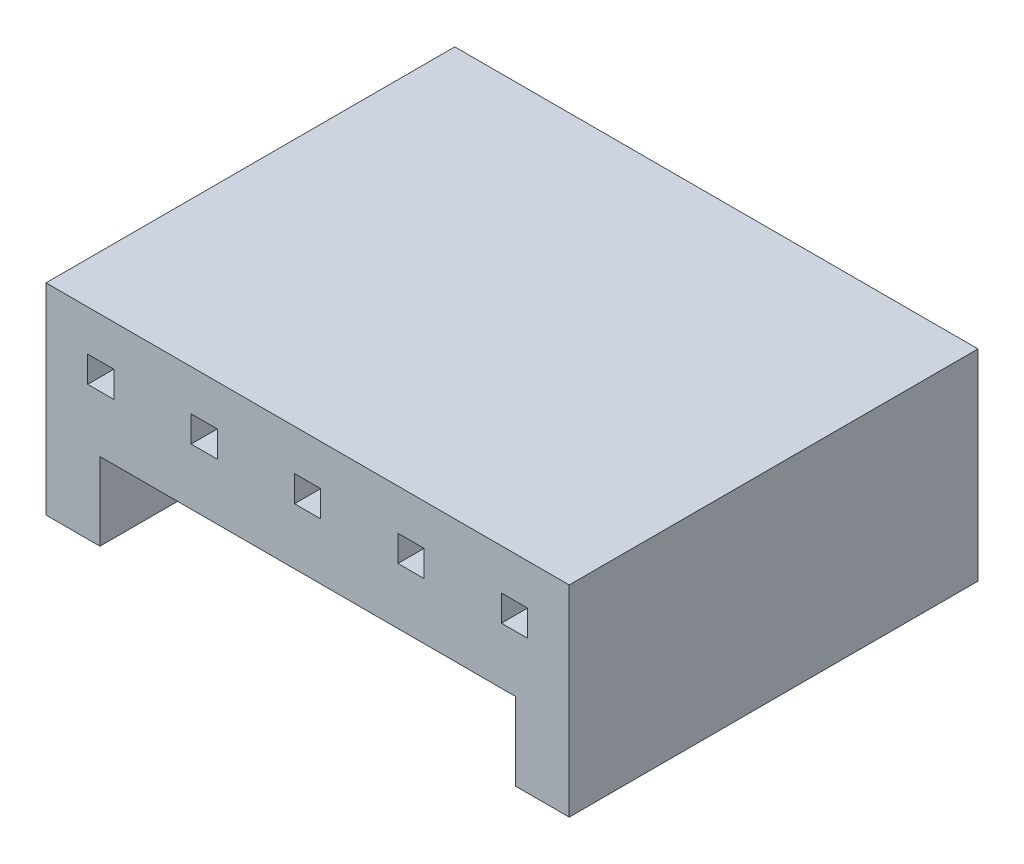
SolidWorks part; units mm, degrees
ref_plane "Front" through (0, 0, 0) normal (0, 0, 1) x (1, 0, 0)
ref_plane "Top" through (0, 0, 0) normal (0, 1, 0) x (1, 0, 0)
ref_plane "Right" through (0, 0, 0) normal (1, 0, 0) x (0, 0, -1)
sketch "Sketch1" plane through (0, 0, 0) normal (0, 0, 1) x (1, 0, 0)
  line L1 (0, 0) -> (12.8, 0)
  line L2 (0, 0) -> (0, 4.92)
  line L3 (0, 4.92) -> (12.8, 4.92)
  line L4 (12.8, 0) -> (12.8, 4.92)
extrude "Boss-Extrude1" add sketch "Sketch1" along normal blind 10
sketch "Sketch2" plane through (0, 0, 10) normal (0, 0, 1) x (1, 0, 0)
  line L0 (0, 4.92) -> (0, 0)
  line L1 (1.02, 3.92) -> (1.02, 3.28)
  line L2 (11.48, 1.9) -> (11.48, 0)
  line L3 (0, 4.92) -> (12.8, 4.92)
  line L4 (1.66, 3.6) -> (3.55, 3.6)
  line L5 (6.08, 3.92) -> (6.08, 3.28)
  line L6 (1.02, 4.92) -> (1.02, 0) construction
  line L7 (1.02, 3.92) -> (1.66, 3.92)
  line L8 (1.02, 3.92) -> (1.02, 3.28)
  line L9 (1.02, 3.28) -> (1.66, 3.28)
  line L10 (1.66, 3.92) -> (1.66, 3.28)
  line L11 (3.55, 3.92) -> (4.19, 3.92)
  line L12 (3.55, 3.92) -> (3.55, 3.28)
  line L13 (3.55, 3.28) -> (4.19, 3.28)
  line L14 (4.19, 3.92) -> (4.19, 3.28)
  line L15 (8.61, 3.92) -> (8.61, 3.28)
  line L16 (6.08, 3.92) -> (6.72, 3.92)
  line L17 (6.08, 3.92) -> (6.08, 3.28)
  line L18 (6.08, 3.28) -> (6.72, 3.28)
  line L19 (6.72, 3.92) -> (6.72, 3.28)
  line L20 (11.14, 3.92) -> (11.14, 3.28)
  line L21 (8.61, 3.92) -> (9.25, 3.92)
  line L22 (8.61, 3.92) -> (8.61, 3.28)
  line L23 (8.61, 3.28) -> (9.25, 3.28)
  line L24 (9.25, 3.92) -> (9.25, 3.28)
  line L25 (12.8, 0) -> (12.8, 3.1033)
  line L26 (11.14, 3.92) -> (11.78, 3.92)
  line L27 (11.14, 3.92) -> (11.14, 3.28)
  line L28 (11.14, 3.28) -> (11.78, 3.28)
  line L29 (11.78, 3.92) -> (11.78, 3.28)
  line L30 (12.8, 0) -> (12.8, 4.92) construction
  line L32 (1.32, 0) -> (11.48, 0)
  line L36 (1.32, 1.9) -> (11.48, 1.9)
  line L37 (1.32, 1.9) -> (1.32, 0)
  point P6 (1.32, 4.92)
  dimension "D4" = 1.89
  dimension "D3" = 1.89
  dimension "D5" = 1.89
  dimension "D1" = 1.02
extrude "Cut-Extrude1" cut sketch "Sketch2" against normal through all
